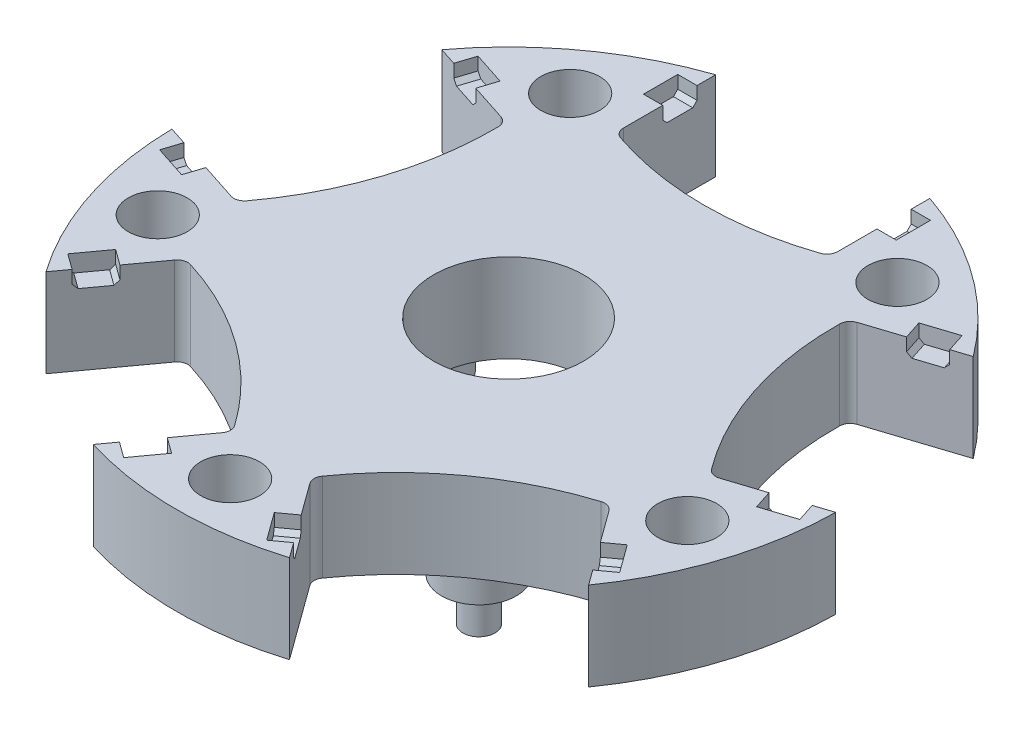
SolidWorks part; units mm, degrees
ref_plane "Front Plane" through (0, 0, 0) normal (0, 0, 1) x (1, 0, 0)
ref_plane "Top Plane" through (0, 0, 0) normal (0, 1, 0) x (1, 0, 0)
ref_plane "Right Plane" through (0, 0, 0) normal (1, 0, 0) x (0, 0, -1)
sketch "Sketch1" plane through (0, 0, 0) normal (0, 1, 0) x (1, 0, 0)
  circle A0 centre (0, 0) radius 31
  circle A1 centre (0, 0) radius 7
  dimension "D1" = 62
  dimension "D2" = 14
extrude "Boss-Extrude1" add sketch "Sketch1" along normal blind 8.25
sketch "Sketch2" plane through (0, 0, 0) normal (0, -1, 0) x (1, 0, 0)
  line L0 (-10, -29.3428) -> (-10, -20.0287)
  line L1 (10, -20.0287) -> (10, -29.3428)
  circle A0 centre (0, 0) radius 31 construction
  arc A1 (-10, -20.0287) -> (10, -20.0287) centre (0, -47.25) cw
  arc A2 (-10, -29.3428) -> (10, -29.3428) centre (0, 0) ccw
  point P10 (0, -31)
  dimension "D2" = 29
  dimension "D1" = 20
  dimension "D3" = 16.25
extrude "Cut-Extrude1" cut sketch "Sketch2" against normal through all
fillet "Fillet1" radius 1 2 edges at (10, 4.125, -20.0287) (-10, 4.125, -20.0287)
pattern_circular "CirPattern2" count 5 over 360 about axis through (0, 0, 0) along (0, 1, 0) of "Cut-Extrude1", "Fillet1"
sketch "Sketch3" plane through (10, 0, 0) normal (-1, 0, 0) x (0, 0, 1)
  line L0 (-27.6, 8.25) -> (-24.4, 8.25)
  line L1 (-29.3428, 8.25) -> (-20.7359, 8.25) construction
  line L2 (-24.4, 8.25) -> (-24.4, 7.05)
  line L3 (-24.8, 6.65) -> (-27.2, 6.65)
  line L4 (-27.6, 7.05) -> (-27.6, 8.25)
  line L7 (-27.2, 6.65) -> (-27.6, 7.05)
  line L8 (-24.4, 7.05) -> (-24.8, 6.65)
  line L9 (-29.3428, 8.25) -> (-29.3428, 0) construction
  point P5 (-24.4, 6.65)
  point P6 (-27.6, 6.65)
  dimension "D1" = 3.2
  dimension "D2" = 1.6
  dimension "D3" = 24.4
  dimension "D4" = 1.7428
extrude "Cut-Extrude2" cut sketch "Sketch3" against normal blind 1.8
mirror "Mirror1" about plane through (0, 0, 0) normal (1, 0, 0) of "Cut-Extrude2"
pattern_circular "CirPattern3" count 5 over 360 about axis through (0, 0, 0) along (0, 1, 0) of "Cut-Extrude2", "Mirror1"
sketch "Sketch5" plane through (0, 0, 0) normal (0, -1, 0) x (1, 0, 0)
  circle A0 centre (0, 26) radius 2.75
  dimension "D1" = 5.5
  dimension "D2" = 26
extrude "Cut-Extrude4" cut sketch "Sketch5" against normal through all
pattern_circular "CirPattern4" count 5 over 360 about axis through (0, 0, 0) along (0, 1, 0) of "Cut-Extrude4"
sketch "Sketch7" plane through (0, 0, 0) normal (0, -1, 0) x (1, 0, 0)
  circle A0 centre (0, 0) radius 15.75
  dimension "D1" = 31.5
extrude "Cut-Extrude5" [suppressed] cut sketch "Sketch7" against normal blind 2
sketch "Sketch8" plane through (0, 0, 0) normal (0, -1, 0) x (1, 0, 0)
  circle A0 centre (0, -12.5) radius 3.5
  dimension "D1" = 7
  dimension "D2" = 12.5
extrude "Boss-Extrude2" add sketch "Sketch8" along normal blind 3.75
sketch "Sketch9" plane through (0, 0, 0) normal (0, -1, 0) x (1, 0, 0)
  circle A0 centre (0, 12.5) radius 2
  dimension "D1" = 4
  dimension "D2" = 12.5
extrude "Cut-Extrude6" cut sketch "Sketch9" against normal blind 4
sketch "Sketch10" plane through (0, -3.75, 0) normal (0, -1, 0) x (1, 0, 0)
  circle A0 centre (0, -12.5) radius 1.5
  dimension "D1" = 3
extrude "Boss-Extrude3" add sketch "Sketch10" along normal blind 4
pattern_circular "CirPattern6" count 5 over 360 about axis through (0, 0, 0) along (0, 1, 0) of "Boss-Extrude2", "Cut-Extrude6", "Boss-Extrude3"
